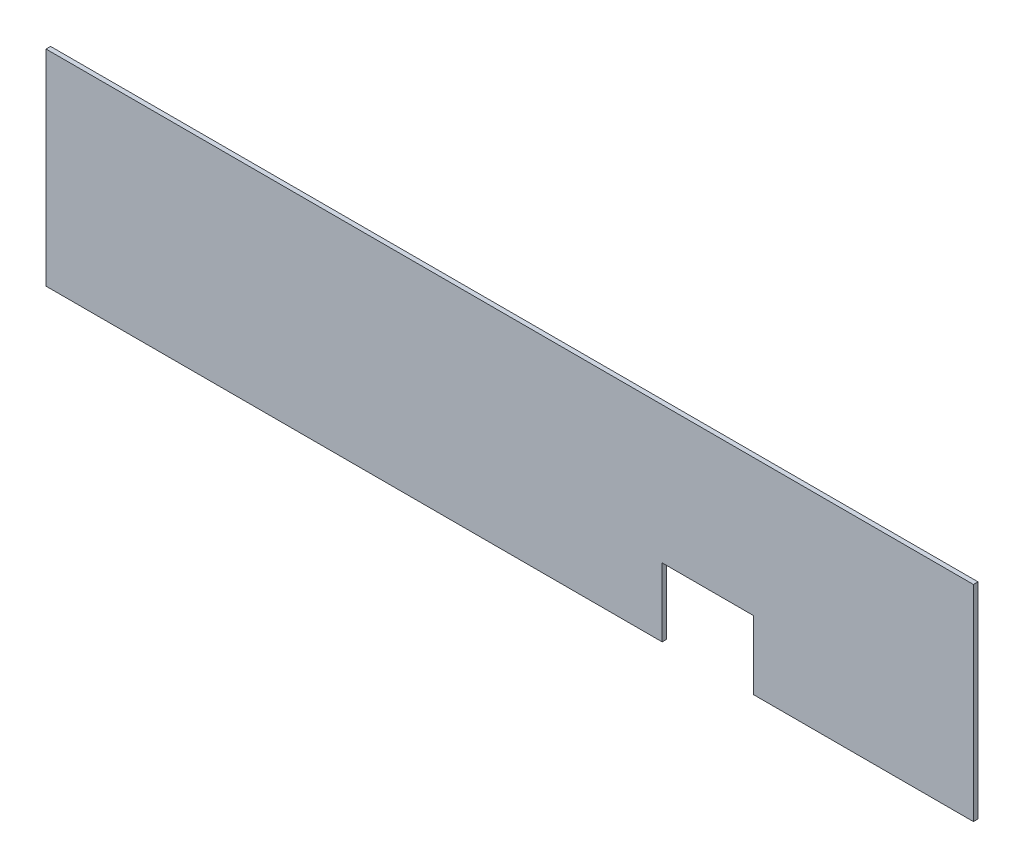
SolidWorks part; units mm, degrees
ref_plane "Front Plane" through (0, 0, 0) normal (0, 0, 1) x (1, 0, 0)
ref_plane "Top Plane" through (0, 0, 0) normal (0, 1, 0) x (1, 0, 0)
ref_plane "Right Plane" through (0, 0, 0) normal (1, 0, 0) x (0, 0, -1)
sketch "Sketch1" plane through (0, 0, 0) normal (0, 0, 1) x (1, 0, 0)
  line L1 (101.6, -22.5) -> (-101.6, -22.5)
  line L2 (101.6, -22.5) -> (101.6, 22.5)
  line L3 (101.6, 22.5) -> (-101.6, 22.5)
  line L4 (-101.6, -22.5) -> (-101.6, 22.5)
  line L5 (101.6, -22.5) -> (-101.6, 22.5) construction
  line L6 (101.6, 22.5) -> (-101.6, -22.5) construction
  point P0 (0, 0)
extrude "Boss-Extrude1" add sketch "Sketch1" along normal blind 1
sketch "Sketch2" plane through (0, 0, 1) normal (0, 0, 1) x (1, 0, 0)
  line L0 (-101.6, -22.5) -> (33.4, -22.5) construction
  line L1 (-101.6, -22.5) -> (101.6, -22.5) construction
  line L2 (33.4, -22.5) -> (33.4, -7.5)
  line L3 (33.4, -7.5) -> (53.4, -7.5)
  line L4 (53.4, -7.5) -> (53.4, -22.5)
  line L5 (53.4, -22.5) -> (33.4, -22.5)
extrude "Cut-Extrude1" cut sketch "Sketch2" against normal blind 1
